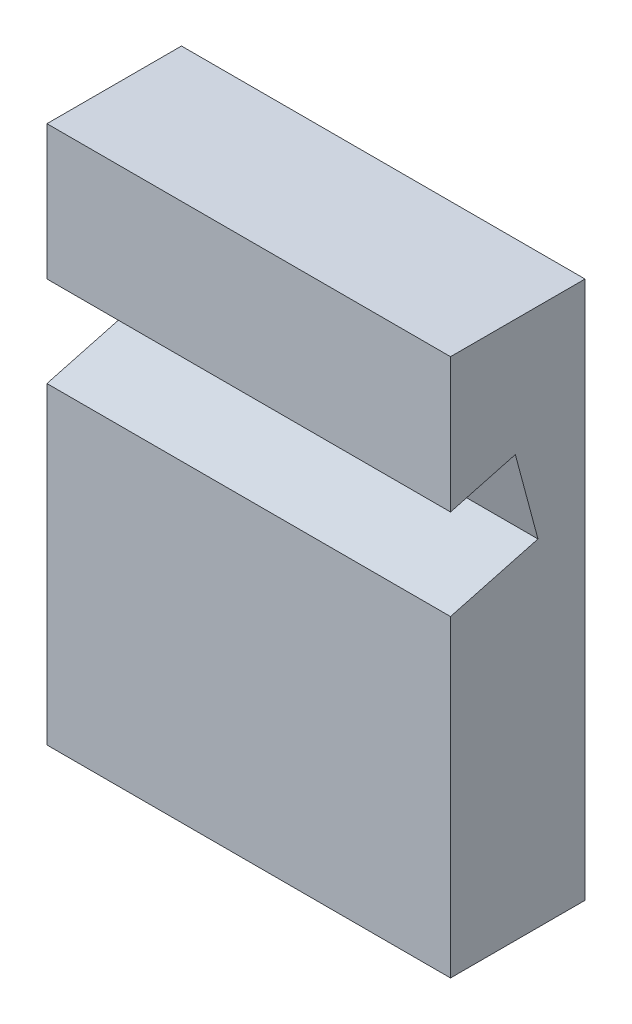
SolidWorks part; units mm, degrees
material "Oak"
ref_plane "Front Plane" through (0, 0, 0) normal (1, 0, 0) x (0, 1, 0)
ref_plane "Top Plane" through (0, 0, 0) normal (0, 0, 1) x (0, 1, 0)
ref_plane "Right Plane" through (0, 0, 0) normal (0, 1, 0) x (-1, 0, 0)
sketch "Sketch1" plane through (0, 0, 0) normal (1, 0, 0) x (0, 1, 0)
  line L0 (0, 0) -> (80, 0)
  line L1 (80, 0) -> (80, 20)
  line L2 (80, 20) -> (60, 20)
  line L3 (60, 20) -> (62.5818, 10.3646)
  line L4 (62.5818, 10.3646) -> (50.0247, 7)
  line L5 (50.0247, 7) -> (46.5414, 20)
  line L6 (46.5414, 20) -> (0, 20)
  line L7 (0, 20) -> (0, 0)
  dimension "D1" = 80
  dimension "D2" = 20
  dimension "D3" = 20
  dimension "D4" = 15
  dimension "D5" = 13
  dimension "D6" = 7
extrude "Boss-Extrude1" add sketch "Sketch1" along normal blind 60
